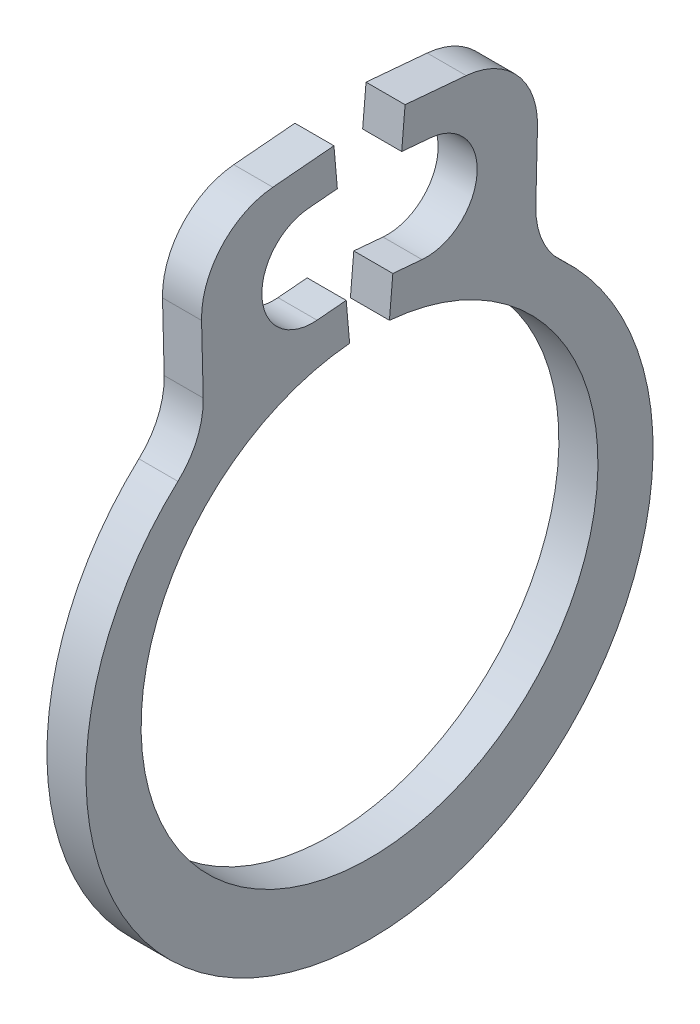
SolidWorks part; units mm, degrees
material "A-Glass Fiber"
ref_plane "Front" through (0, 0, 0) normal (0, 0, 1) x (1, 0, 0)
ref_plane "Top" through (0, 0, 0) normal (0, 1, 0) x (1, 0, 0)
ref_plane "Right" through (0, 0, 0) normal (1, 0, 0) x (0, 0, -1)
sketch "Sketch1" plane through (0, 0, 0) normal (1, 0, 0) x (0, 0, -1)
  line L0 (0, 0) -> (0, 1.4859) construction
  line L1 (-0.1295, 1.4802) -> (-0.2313, 2.6442) construction
  line L2 (0.2313, 2.6442) -> (1.1043, 2.5678)
  line L3 (1.1043, 2.5678) -> (1.0756, 1.3998)
  line L4 (0.1295, 1.4802) -> (0.2313, 2.6442) construction
  line L5 (-0.2313, 2.6442) -> (-1.1043, 2.5678)
  line L6 (-1.1043, 2.5678) -> (-1.0756, 1.3998)
  line L7 (-1.0756, 1.3998) -> (-0.9054, 1.1782) construction
  line L8 (1.0756, 1.3998) -> (0.9054, 1.1782) construction
  line L9 (0, -1.4859) -> (0, -1.9431) construction
  line L10 (-1.1043, 2.5678) -> (-0.1295, 1.4802) construction
  line L11 (0, 1.4859) -> (0, 2.6543) construction
  line L12 (0.1516, 1.7333) -> (0.3414, 1.7167)
  line L13 (0.2092, 2.3912) -> (0.399, 2.3746)
  line L14 (0.1516, 1.7333) -> (0.1295, 1.4802)
  line L15 (0.2092, 2.3912) -> (0.2313, 2.6442)
  line L16 (-0.2092, 2.3912) -> (-0.399, 2.3746)
  line L17 (-0.1516, 1.7333) -> (-0.3414, 1.7167)
  line L18 (-0.1516, 1.7333) -> (-0.1295, 1.4802)
  line L19 (-0.2092, 2.3912) -> (-0.2313, 2.6442)
  line L20 (-1.4859, 0) -> (1.4859, 0) construction
  circle A0 centre (0, 0) radius 1.4859 construction
  arc A1 (-0.1295, 1.4802) -> (0.1295, 1.4802) centre (0, 0) ccw
  arc A2 (0.3414, 1.7167) -> (0.399, 2.3746) centre (0.3702, 2.0456) ccw
  circle A3 centre (0, 0) radius 2.7178 construction
  arc A4 (-0.3414, 1.7167) -> (-0.399, 2.3746) centre (-0.3702, 2.0456) cw
  arc A6 (-1.0756, 1.3998) -> (1.0756, 1.3998) centre (0, -0.0986) ccw
  point P0 (0, -1.9431)
  dimension "A" = 2.9718
  dimension "Smin" = 0.2794
  dimension "H" = 1.1684
  dimension "D2" = 0.8763
  dimension "Angle" = 5
  dimension "R" = 0.6604
extrude "Extrude1" add sketch "Sketch1" along normal mid plane 0.254
fillet "Fillet1" radius 0.508 4 edges at (0, 1.3998, 1.0756) (0, 1.3998, -1.0756) (0, 2.5678, 1.1043) (0, 2.5678, -1.1043)
sketch "Sketch2" plane through (0, 0, 0) normal (0, 0, 1) x (1, 0, 0)
  line L0 (-1.4224, 0) -> (3.6576, 0)
  line L1 (3.6576, 0) -> (3.6576, -1.5875)
  line L2 (-0.1524, -1.5875) -> (-1.3208, -1.5875)
  line L3 (3.6576, -1.5875) -> (0.1524, -1.5875)
  line L4 (0.1524, -1.5875) -> (0.1524, -1.4859)
  line L5 (0.1524, -1.4859) -> (-0.1524, -1.4859)
  line L6 (-0.1524, -1.4859) -> (-0.1524, -1.5875)
  line L7 (-0.1524, -1.5875) -> (-1.4224, -1.5875) construction
  line L8 (-1.4224, -1.5875) -> (-1.4224, 0) construction
  line L9 (3.6576, 0) -> (76.391, 0) construction
  line L10 (-1.3208, -1.5875) -> (-1.4224, -1.4859)
  line L11 (-1.4224, -1.4859) -> (-1.4224, 0)
  point P10 (0, -1.4859)
  dimension "D2" = 5.08
  dimension "D3" = 1.27
  dimension "D1" = 45
revolve "Revolve1" [suppressed] add sketch "Sketch2" angle 360 about L9
delete or keep bodies "Body-Delete1" [suppressed] type delete bodies bodies 122
equation "\"D2@Sketch2\" = \"D1@Extrude1\"*20"
equation "\"D3@Sketch2\" = \"D2@Sketch2\"/4"
equation "\"D2@Sketch1\" = \"H@Sketch1\"*.75"
equation "\"D1@Fillet1\" = \"D1@Extrude1\"*2"
